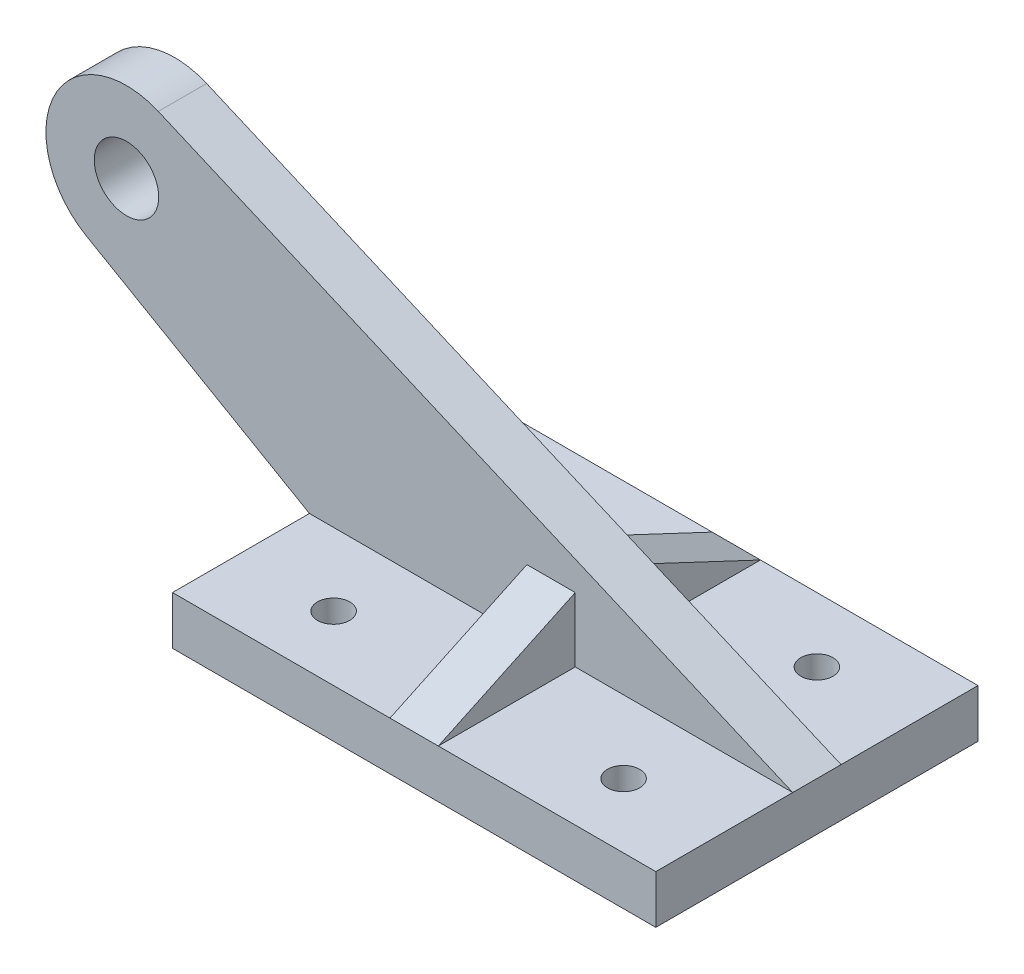
SolidWorks part; units mm, degrees
ref_plane "Front Plane" through (0, 0, 0) normal (0, 0, 1) x (1, 0, 0)
ref_plane "Top Plane" through (0, 0, 0) normal (0, 1, 0) x (1, 0, 0)
ref_plane "Right Plane" through (0, 0, 0) normal (1, 0, 0) x (0, 0, -1)
sketch "Sketch1" plane through (0, 0, 0) normal (0, 1, 0) x (1, 0, 0)
  line L1 (-75, 50) -> (75, 50)
  line L2 (-75, 50) -> (-75, -50)
  line L3 (-75, -50) -> (75, -50)
  line L4 (75, 50) -> (75, -50)
  line L5 (-75, 50) -> (75, -50) construction
  line L6 (-75, -50) -> (75, 50) construction
  point P0 (0, 0)
  dimension "D1" = 150
  dimension "D2" = 100
extrude "Boss-Extrude1" add sketch "Sketch1" along normal blind 15
sketch "Sketch2" plane through (0, 15, 0) normal (0, 1, 0) x (1, 0, 0)
  line L0 (75, -50) -> (75, 50) construction
  line L1 (-100.7951, 0) -> (112.6877, 0) construction
  line L2 (-75, -50) -> (75, -50) construction
  circle A0 centre (45, -30) radius 5
  circle A1 centre (45, 30) radius 5
  circle A2 centre (-45, 30) radius 5
  circle A3 centre (-45, -30) radius 5
  dimension "D1" = 10
  dimension "D6" = 60
  dimension "D2" = 30
  dimension "D3" = 20
  dimension "D7" = 90
  dimension "D4" = 2
  dimension "D5" = 2
extrude "Cut-Extrude2" cut sketch "Sketch2" against normal blind 15
ref_plane "Plane2" through (0, 0, 0) normal (0, 0, 1) x (1, 0, 0)
sketch "Sketch4" plane through (0, 0, 0) normal (0, 0, 1) x (1, 0, 0)
  line L0 (75, 15) -> (-75, 15)
  line L1 (-75, 15) -> (-144.282, 55)
  line L2 (75, 15) -> (-121.9115, 99.6196)
  arc A0 (-121.9115, 99.6196) -> (-144.282, 55) centre (-131.782, 76.6506) ccw
  circle A1 centre (-131.782, 76.6506) radius 10
  dimension "D3" = 50
  dimension "D4" = 20
  dimension "D1" = 80
  dimension "D2" = 150
extrude "Boss-Extrude3" add sketch "Sketch4" along normal mid plane 15
sketch "Sketch5" plane through (0, 0, 0) normal (1, 0, 0) x (0, 0, -1)
  line L0 (-7.5, 15) -> (-7.5, 35)
  line L1 (-7.5, 15) -> (-7.5, 99.6196) construction
  line L2 (-7.5, 35) -> (-50, 15)
  line L3 (-50, 15) -> (-7.5, 15)
  dimension "D1" = 20
extrude "Boss-Extrude4" add sketch "Sketch5" along normal mid plane 15
sketch "Sketch6" plane through (0, 0, 0) normal (1, 0, 0) x (0, 0, -1)
  line L0 (7.5, 15) -> (7.5, 35)
  line L1 (7.5, 15) -> (7.5, 99.6196) construction
  line L2 (7.5, 35) -> (50, 15)
  line L3 (50, 15) -> (7.5, 15)
  dimension "D1" = 20
extrude "Boss-Extrude5" add sketch "Sketch6" along normal mid plane 15
